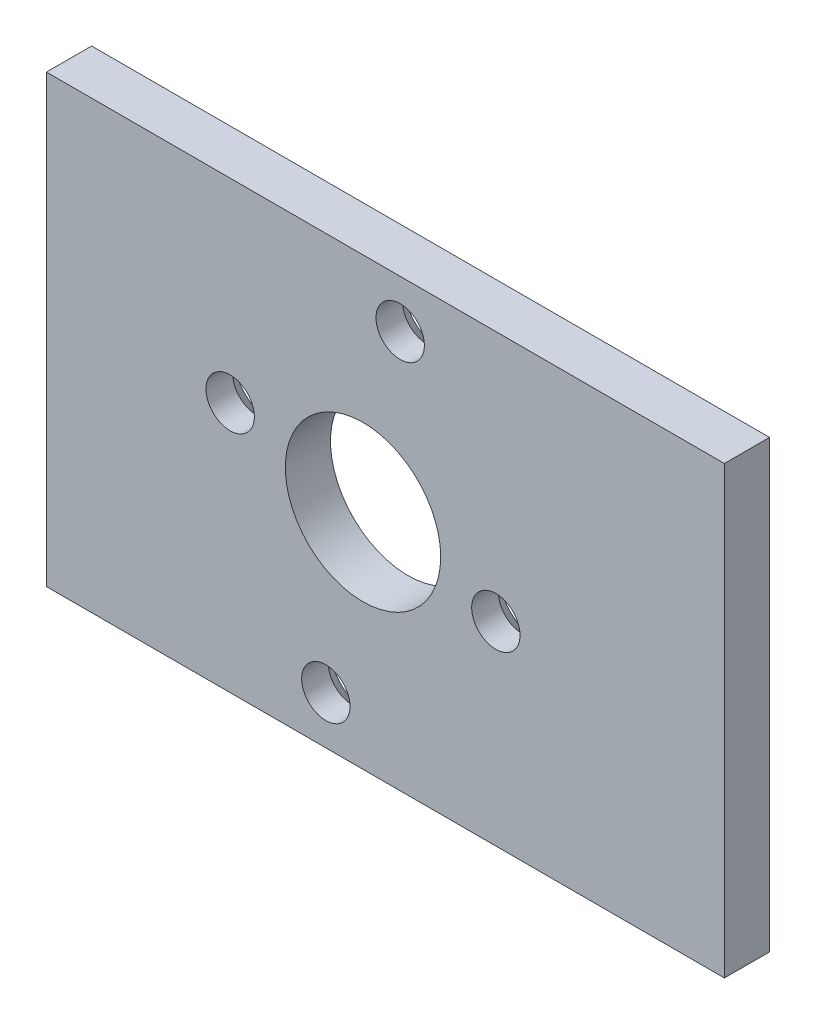
SolidWorks part; units mm, degrees
material "6061 Alloy"
ref_plane "Front Plane" through (0, 0, 0) normal (0, 0, 1) x (1, 0, 0)
ref_plane "Top Plane" through (0, 0, 0) normal (0, 1, 0) x (1, 0, 0)
ref_plane "Right Plane" through (0, 0, 0) normal (1, 0, 0) x (0, 0, -1)
sketch "Sketch1" plane through (0, 0, 0) normal (0, 0, 1) x (1, 0, 0)
  line L0 (9.3364, -1.9845) -> (-9.3364, 1.9845) construction
  line L1 (-22.2504, -15.6591) -> (25.4, -15.6591)
  line L2 (-25.4, -15.6591) -> (-25.4, 15.6591) construction
  line L3 (-22.2504, 15.6591) -> (25.4, 15.6591)
  line L4 (25.4, -15.6591) -> (25.4, 15.6591)
  line L5 (-25.4, -15.6591) -> (25.4, 15.6591) construction
  line L6 (-25.4, 15.6591) -> (25.4, -15.6591) construction
  line L7 (-2.6134, -12.2953) -> (2.6134, 12.2953) construction
  line L8 (0, -1000) -> (0, 49000) construction
  line L10 (-22.2504, 15.6591) -> (-22.2504, -15.6591)
  circle A0 centre (9.3364, -1.9845) radius 1.7
  circle A1 centre (-9.3364, 1.9845) radius 1.7
  circle A2 centre (2.6134, 12.2953) radius 1.7
  circle A3 centre (-2.6134, -12.2953) radius 1.7
  circle A4 centre (0, 0) radius 5.461
  point P0 (0, 0)
  dimension "D2" = 10.922
  dimension "D1" = 3.4
  dimension "D3" = 31.3182
  dimension "D4" = 50.8
  dimension "D5" = 25.14
  dimension "D6" = 19.09
  dimension "D7" = 102
  dimension "D8" = 3.1496
extrude "Boss-Extrude1" add sketch "Sketch1" along normal blind 3.175
chamfer "Chamfer1" distance 1.3 angle 45 4 edges at (-0.9134, -12.2953, 0) (11.0364, -1.9845, 0) (4.3134, 12.2953, 0) (-7.6364, 1.9845, 0)
